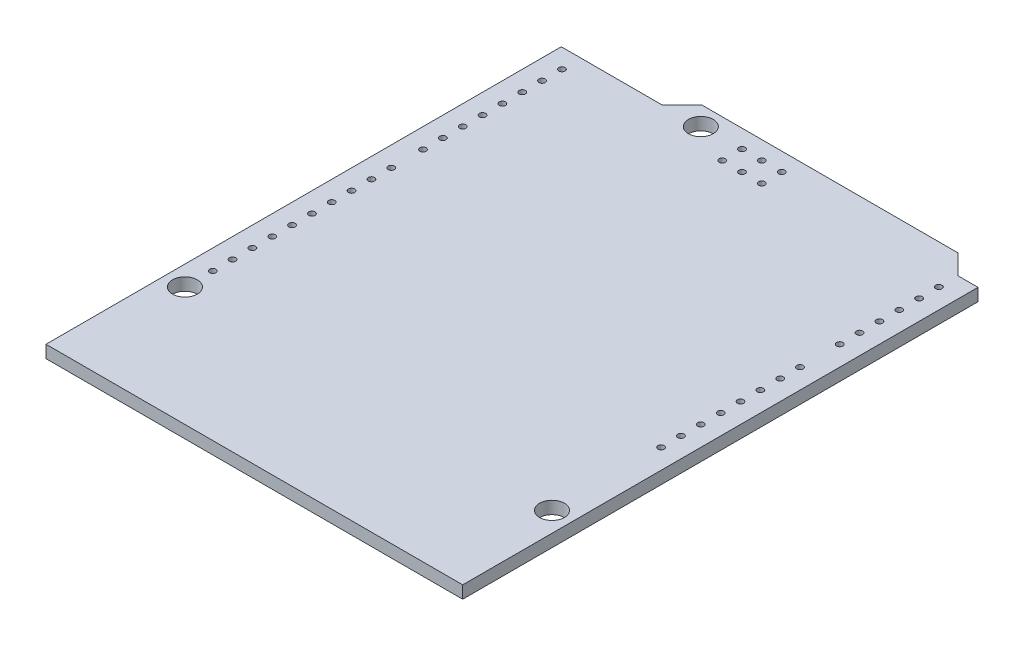
SolidWorks part; units mm, degrees
material "E-Glass Fiber"
ref_plane "Front Plane" through (0, 0, 0) normal (0, 0, 1) x (1, 0, 0)
ref_plane "Top Plane" through (0, 0, 0) normal (0, 1, 0) x (1, 0, 0)
ref_plane "Right Plane" through (0, 0, 0) normal (1, 0, 0) x (0, 0, -1)
sketch "Sketch1" plane through (0, 0, 0) normal (0, 1, 0) x (1, 0, 0)
  line L0 (-29.337, 0) -> (29.337, 0) construction
  line L1 (0, 0) -> (-53.34, 0)
  line L2 (0, 0) -> (0, 65.96)
  line L3 (-5.08, 68.5) -> (-37.846, 68.5)
  line L4 (-53.34, 0) -> (-53.34, 65.96)
  line L5 (-53.34, 65.96) -> (-40.386, 65.96)
  line L6 (-40.386, 65.96) -> (-37.846, 68.5)
  line L7 (-5.08, 68.5) -> (-2.54, 65.96)
  line L8 (-2.54, 65.96) -> (0, 65.96)
  circle A1 centre (-35.56, 66.04) radius 1.5875
  circle A2 centre (-2.54, 13.97) radius 1.5875
  circle A3 centre (-50.8, 15.24) radius 1.5875
  dimension "D1" = 68.5
  dimension "D2" = 53.34
  dimension "D4" = 2.54
  dimension "D5" = 45
  dimension "D6" = 45
  dimension "D7" = 40.386
  dimension "D9" = 66.04
  dimension "D10" = 35.56
  dimension "D12" = 13.97
  dimension "D13" = 2.54
  dimension "D14" = 15.24
  dimension "D15" = 50.8
  dimension "D18" = 2.54
extrude "Boss-Extrude1" add sketch "Sketch1" against normal blind 1.6
sketch "Sketch2" plane through (0, 0, 0) normal (0, 1, 0) x (1, 0, 0)
  line L0 (0, -37.675) -> (0, 37.675) construction
  line L1 (-29.337, 0) -> (29.337, 0) construction
  circle A0 centre (-2.54, 27.94) radius 0.4
  dimension "D1" = 0.8
  dimension "D2" = 2.54
  dimension "D3" = 27.94
extrude "Cut-Extrude1" cut sketch "Sketch2" against normal blind 1.65
sketch "Sketch3" plane through (0, 0, 0) normal (0, 1, 0) x (1, 0, 0)
  line L0 (0, -37.675) -> (0, 37.675) construction
  line L1 (-29.337, 0) -> (29.337, 0) construction
  circle A0 centre (-50.8, 18.796) radius 0.4
  dimension "D2" = 0.8
  dimension "D1" = 50.8
  dimension "D3" = 18.796
extrude "Cut-Extrude2" cut sketch "Sketch3" against normal blind 1.65
pattern_linear "LPattern1" count 15 spacing 2.54 along (0, 0, -1) skipping (8, 0) of "Cut-Extrude1"
sketch "Sketch4" plane through (0, 0, 0) normal (0, 1, 0) x (1, 0, 0)
  line L0 (-29.337, 0) -> (29.337, 0) construction
  line L1 (0, -37.675) -> (0, 37.675) construction
  circle A0 centre (-50.8, 45.72) radius 0.4
  dimension "D3" = 0.8
  dimension "D1" = 45.72
  dimension "D2" = 50.8
extrude "Cut-Extrude3" cut sketch "Sketch4" against normal blind 1.65
pattern_linear "LPattern2" count 10 spacing 2.54 along (0, 0, -1) of "Cut-Extrude2"
pattern_linear "LPattern3" count 17 spacing 2.54 along (0, 0, -1) skipping (8, 0) of "Cut-Extrude3"
sketch "Sketch5" plane through (0, 0, 0) normal (0, 1, 0) x (1, 0, 0)
  line L0 (-27.89, 66.18) -> (-27.89, 63.64) construction
  line L1 (-30.43, 66.18) -> (-25.35, 66.18) construction
  line L2 (-30.43, 66.18) -> (-30.43, 63.64) construction
  line L3 (-30.43, 63.64) -> (-25.35, 63.64) construction
  line L4 (-25.35, 66.18) -> (-25.35, 63.64) construction
  line L5 (-29.337, 0) -> (29.337, 0) construction
  line L6 (0, -37.675) -> (0, 37.675) construction
  circle A0 centre (-30.43, 66.18) radius 0.4
  circle A1 centre (-27.89, 66.18) radius 0.4
  circle A2 centre (-25.35, 66.18) radius 0.4
  circle A3 centre (-25.35, 63.64) radius 0.4
  circle A4 centre (-27.89, 63.64) radius 0.4
  circle A5 centre (-30.43, 63.64) radius 0.4
  dimension "D4" = 0.8
  dimension "D1" = 2.54
  dimension "D2" = 2.54
  dimension "D3" = 2.54
  dimension "D5" = 63.64
  dimension "D6" = 30.43
extrude "Cut-Extrude4" cut sketch "Sketch5" against normal blind 10
